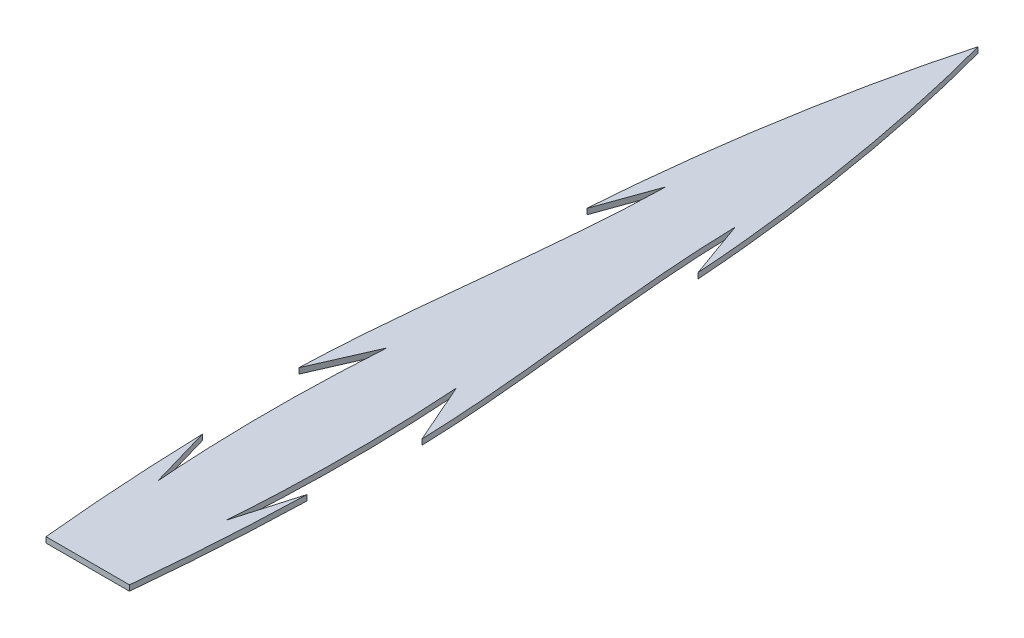
SolidWorks part; units mm, degrees
ref_plane "Front Plane" through (0, 0, 0) normal (0, 0, 1) x (1, 0, 0)
ref_plane "Top Plane" through (0, 0, 0) normal (0, 1, 0) x (1, 0, 0)
ref_plane "Right Plane" through (0, 0, 0) normal (1, 0, 0) x (0, 0, -1)
sketch "Sketch1" plane through (0, 0, 0) normal (0, 1, 0) x (1, 0, 0)
  line L0 (0, 0) -> (0, 101.6)
  line L1 (-68.2771, 0) -> (-68.2771, 12.7)
  line L2 (-92.486, 0) -> (-92.486, 19.05)
  line L3 (-115.9222, 0) -> (-115.9222, 38.1)
  line L4 (-133.435, 0) -> (-133.435, 31.75)
  line L5 (-146.8272, 0) -> (-146.8272, 69.85)
  line L6 (-163.0523, 0) -> (-163.0523, 65.0875)
  line L7 (-4.7625, 0) -> (4.7625, 0)
  line L8 (7.0291, 31.1235) -> (3.9688, 38.1)
  line L9 (6.342, 63.3062) -> (3.9688, 69.9329)
  line L14 (-6.342, 63.3062) -> (-3.9688, 69.9329)
  line L15 (-7.0291, 31.1235) -> (-3.9688, 38.1)
  spline S0 degree 3 poles (0, 101.6) (-3.2916, 89.5537) (-5.5079, 75.6315) (-6.342, 63.3062) knots 0 0 0 0 1 1 1 1
  spline S1 degree 3 poles (-3.9688, 69.9329) (-4.2265, 57.2245) (-6.6454, 43.8634) (-7.0291, 31.1235) knots 0 0 0 0 1 1 1 1
  spline S2 degree 2 poles (-4.7625, 0) (-5.7064, 9.5095) (-5.969, 19.05) knots 0 0 0 1 1 1
  spline S3 degree 2 poles (-3.8899, 11.8767) (-5.0375, 15.7087) (-5.969, 19.05) knots 0 0 0 1 1 1
  spline S4 degree 2 poles (-3.9688, 38.1) (-4.8679, 24.5452) (-3.8899, 11.8767) knots 0 0 0 1 1 1
  spline S5 degree 2 poles (3.9688, 38.1) (4.8679, 24.5452) (3.8899, 11.8767) knots 0 0 0 1 1 1
  spline S6 degree 2 poles (3.8899, 11.8767) (5.0375, 15.7087) (5.969, 19.05) knots 0 0 0 1 1 1
  spline S7 degree 2 poles (4.7625, 0) (5.7064, 9.5095) (5.969, 19.05) knots 0 0 0 1 1 1
  spline S8 degree 3 poles (3.9688, 69.9329) (4.2265, 57.2245) (6.6454, 43.8634) (7.0291, 31.1235) knots 0 0 0 0 1 1 1 1
  spline S9 degree 3 poles (0, 101.6) (3.2916, 89.5537) (5.5079, 75.6315) (6.342, 63.3062) knots 0 0 0 0 1 1 1 1
  dimension "D1" = 101.6
  dimension "D2" = 12.7
  dimension "D3" = 19.05
  dimension "D4" = 38.1
  dimension "D5" = 31.75
  dimension "D6" = 69.85
  dimension "D7" = 65.0875
  dimension "D8" = 9.525
  dimension "D15" = 0
extrude "Boss-Extrude1" add sketch "Sketch1" along normal blind 0.635 contours L15 S4 S3 S2 L7 L0 S0 L14 S1 | S9 L0 L7 S7 S6 S5 L8 S8 L9
